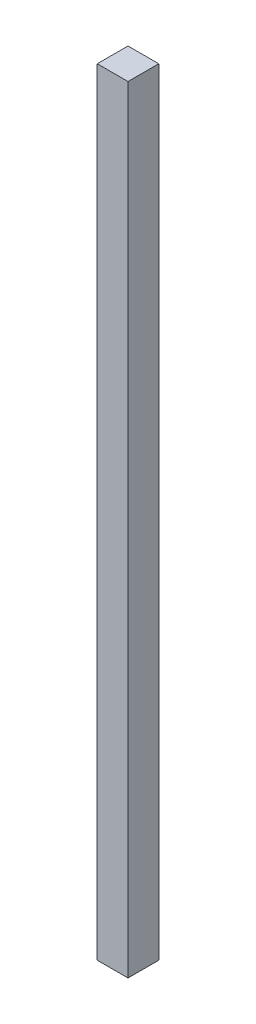
SolidWorks part; units mm, degrees
ref_plane "Front Plane" through (0, 0, 0) normal (0, 0, 1) x (1, 0, 0)
ref_plane "Top Plane" through (0, 0, 0) normal (0, 1, 0) x (1, 0, 0)
ref_plane "Right Plane" through (0, 0, 0) normal (1, 0, 0) x (0, 0, -1)
sketch "Sketch2" plane through (0, 0, 0) normal (0, 1, 0) x (1, 0, 0)
  line L1 (-38.1, 38.1) -> (38.1, 38.1)
  line L2 (-38.1, 38.1) -> (-38.1, -38.1)
  line L3 (-38.1, -38.1) -> (38.1, -38.1)
  line L4 (38.1, 38.1) -> (38.1, -38.1)
  line L5 (-38.1, 38.1) -> (38.1, -38.1) construction
  line L6 (-38.1, -38.1) -> (38.1, 38.1) construction
  point P0 (0, 0)
  dimension "D1" = 76.2
  dimension "D2" = 76.2
extrude "Boss-Extrude1" add sketch "Sketch2" along normal blind 1923.8
